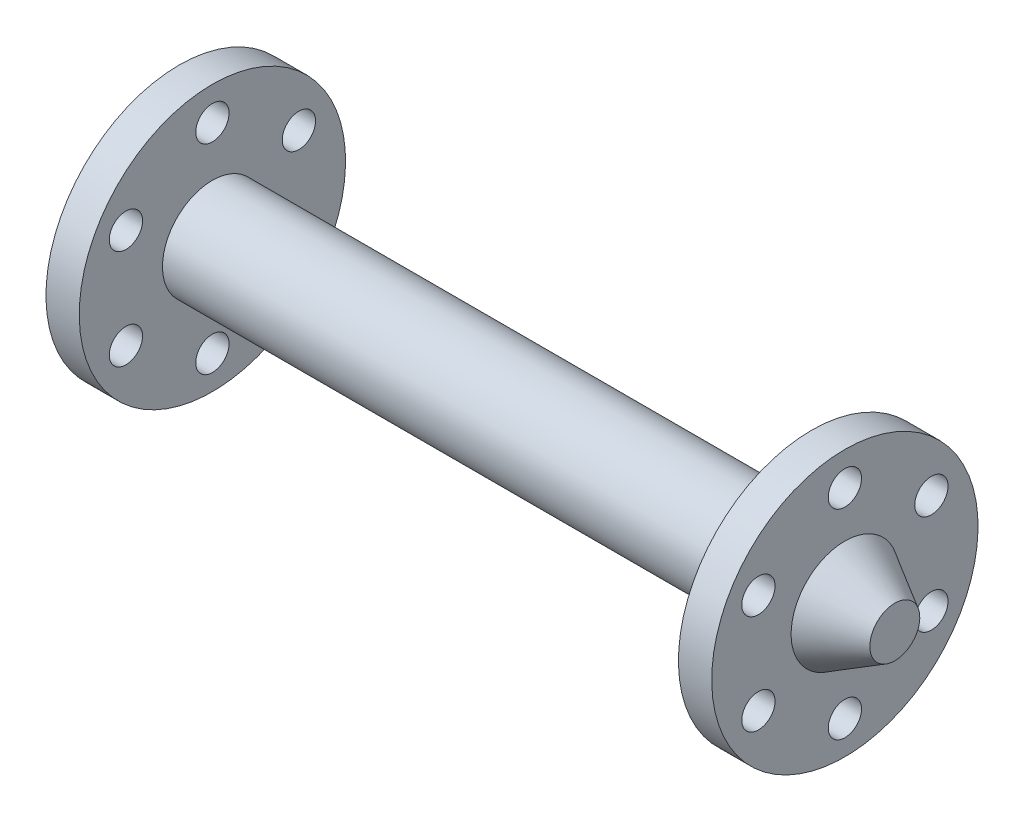
SolidWorks part; units mm, degrees
ref_plane "Front Plane" through (0, 0, 0) normal (0, 0, 1) x (1, 0, 0)
ref_plane "Top Plane" through (0, 0, 0) normal (0, 1, 0) x (1, 0, 0)
ref_plane "Right Plane" through (0, 0, 0) normal (1, 0, 0) x (0, 0, -1)
sketch "Sketch1" plane through (0, 0, 0) normal (0, 0, 1) x (1, 0, 0)
  line L0 (-230, 0) -> (-230, 15)
  line L1 (-230, 15) -> (-200, 32.3205)
  line L2 (-200, 32.3205) -> (-200, 80)
  line L3 (-200, 80) -> (-180, 80)
  line L4 (-180, 80) -> (-180, 30)
  line L5 (-180, 30) -> (180, 30)
  line L6 (180, 30) -> (180, 80)
  line L7 (180, 80) -> (200, 80)
  line L8 (200, 80) -> (200, 32.3205)
  line L9 (200, 32.3205) -> (230, 15)
  line L10 (230, 15) -> (230, 0)
  line L11 (230, 0) -> (-230, 0)
  dimension "D1" = 15
  dimension "D2" = 80
  dimension "D3" = 30
  dimension "D4" = 20
  dimension "D5" = 30
  dimension "D6" = 30
  dimension "D7" = 30
  dimension "D8" = 460
  dimension "D9" = 230
  dimension "D10" = 80
revolve "Revolve1" add sketch "Sketch1" angle 360 about L11
sketch "Sketch2" plane through (-200, 0, 0) normal (-1, 0, 0) x (0, 0, 1)
  circle A0 centre (0, 0) radius 60 construction
  point P5 (0, 60)
  dimension "D1" = 120
hole_wizard "Ø1.0mm Dowel Hole1" positions "Sketch2" profile "Sketch3" hole size "Ø1.0" standard "ISO" end condition through all
sketch "Sketch3" plane through (-200, 60, 0) normal (0, 1, 0) x (0, 0, 1)
  line L0 (0, 0) -> (0, 430)
  line L1 (0, 430) -> (10, 430)
  line L2 (10, 430) -> (10, 0)
  line L5 (10, 0) -> (0, 0)
  line L11 (0, -6.35) -> (0, 107.95) construction
  dimension "Thru Hole Dia." = 20
  dimension "Thru Hole Depth" = 430
pattern_circular "CirPattern1" count 6 over 360 about axis through (0, 0, 0) along (1, 0, 0) of "Ø1.0mm Dowel Hole1"
